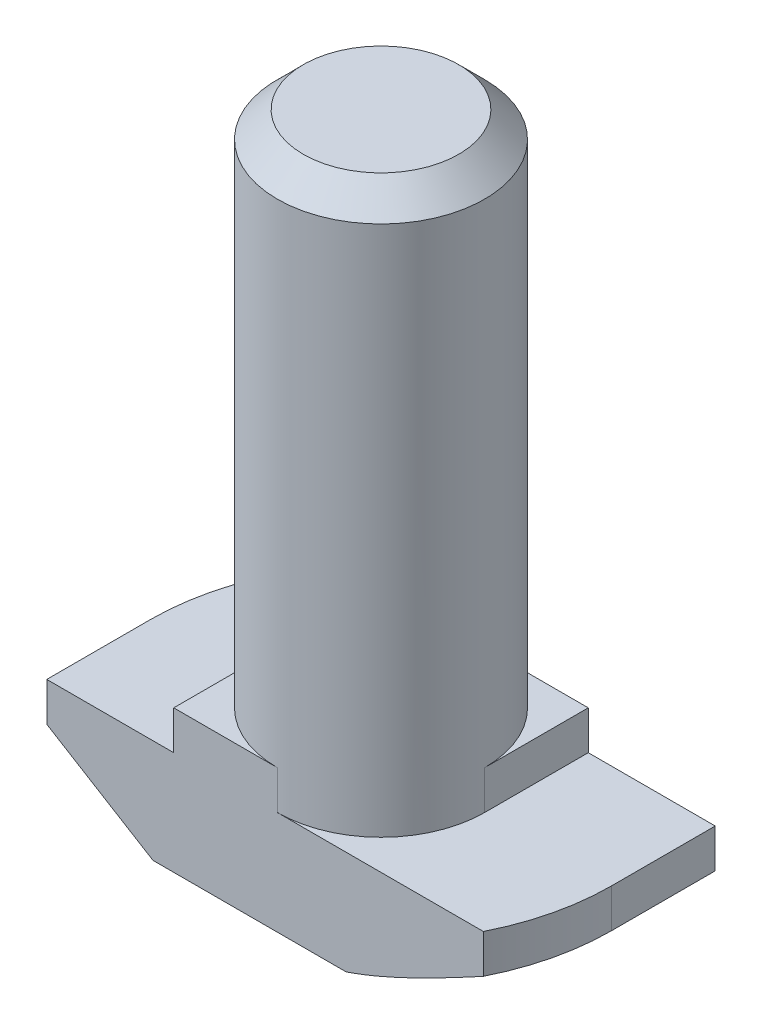
SolidWorks part; units mm, degrees
ref_plane "Спереди" through (0, 0, 0) normal (0, 0, 1) x (1, 0, 0)
ref_plane "Сверху" through (0, 0, 0) normal (0, 1, 0) x (1, 0, 0)
ref_plane "Справа" through (0, 0, 0) normal (1, 0, 0) x (0, 0, -1)
sketch "Эскиз1" plane through (0, 0, 0) normal (0, 0, 1) x (1, 0, 0)
  line L0 (8.9, 0) -> (-8.9, 0)
  line L1 (-8.9, 0) -> (-8.9, 4)
  line L2 (-8.9, 4) -> (-4, 4)
  line L3 (-4, 4) -> (-4, 5.5)
  line L4 (-4, 5.5) -> (4, 5.5)
  line L5 (0, 5.5) -> (0, 0) construction
  line L6 (4, 4) -> (4, 5.5)
  line L7 (8.9, 4) -> (4, 4)
  line L8 (8.9, 0) -> (8.9, 4)
  point P12 (-8.25, 2.6435)
  point P13 (-4, 3.6993)
  dimension "D1" = 8
  dimension "D2" = 17.8
  dimension "D3" = 5.5
  dimension "D4" = 1.5
extrude "Бобышка-Вытянуть1" add sketch "Эскиз1" along normal mid plane 8
sketch "Эскиз3" plane through (0, 5.5, 0) normal (0, 1, 0) x (1, 0, 0)
  line L1 (4, 4) -> (-4, 4) construction
  line L2 (-4, 0) -> (-4, 4)
  line L3 (-4, 4) -> (0, 4)
  line L4 (0, -4) -> (4, -4)
  line L5 (4, -4) -> (-4, -4) construction
  line L6 (4, -4) -> (4, 0)
  line L7 (4, -4) -> (4, 4) construction
  arc A0 (-4, 0) -> (0, 4) centre (0, 0) cw
  arc A1 (4, 0) -> (0, -4) centre (0, 0) cw
extrude "Вырез-Вытянуть1" cut sketch "Эскиз3" against normal up to surface (1.5 mm away) up to face at (-6.45, 4, 0)
sketch "Эскиз2" plane through (0, 5.5, 0) normal (0, 1, 0) x (1, 0, 0)
  circle A0 centre (0, 0) radius 4
  dimension "D1" = 8
extrude "Бобышка-Вытянуть2" add sketch "Эскиз2" along normal blind 20
cosmetic thread "Условное изображение резьбы1" parameters "D1"=20, "D2"=6.619
sketch "Эскиз4" plane through (0, 4, 0) normal (0, 1, 0) x (1, 0, 0)
  line L0 (-8.9, -4) -> (-8.9, 4) construction
  line L1 (8.9, -4) -> (8.9, 4) construction
  line L2 (-7.9505, 4) -> (-8.9, 4)
  line L3 (-8.9, 4) -> (-8.9, 0)
  line L4 (7.9505, -4) -> (8.9, -4)
  line L5 (8.9, -4) -> (8.9, 0)
  arc A0 (-8.9, 0) -> (-7.9505, 4) centre (0, 0) cw
  arc A1 (8.9, 0) -> (7.9505, -4) centre (0, 0) cw
extrude "Вырез-Вытянуть2" cut sketch "Эскиз4" against normal through all
sketch "Эскиз5" plane through (0, 0, 4) normal (0, 0, 1) x (1, 0, 0)
  line L0 (-8.9, 2.5) -> (-4.8, 0)
  line L1 (-8.9, 4) -> (-8.9, 0) construction
  line L2 (-8.9, 0) -> (7.9505, 0) construction
  line L3 (-4.8, 0) -> (-8.9, 0)
  line L4 (-8.9, 0) -> (-8.9, 2.5)
  line L6 (-4, 4) -> (-8.9, 4) construction
  line L7 (-4, 5.5) -> (-4, 4) construction
  point P6 (-4.9519, 0)
  point P9 (0, 0)
  point P10 (-4.6154, 0)
  point P12 (-8.25, 2.2665)
  point P15 (0, 0)
  dimension "D1" = 1.5
  dimension "D2" = 0.8
sketch "Эскиз6" plane through (0, 0, 0) normal (0, -1, 0) x (1, 0, 0)
  line L0 (0, -8.9) -> (8.9, -8.9)
  line L1 (8.9, -8.9) -> (8.9, 0)
  line L2 (0, 8.9) -> (-8.9, 8.9)
  line L3 (-8.9, 8.9) -> (-8.9, 0)
  arc A0 (-8.9, 0) -> (0, -8.9) centre (0, 0) ccw
  arc A1 (8.9, 0) -> (0, 8.9) centre (0, 0) ccw
  point P10 (0, 0)
sweep "Вырез-По траектории1" cut profiles "Эскиз5" path "Эскиз6"
chamfer "Фаска2" distance 1 angle 45 1 edges at (0, 25.5, 4)
